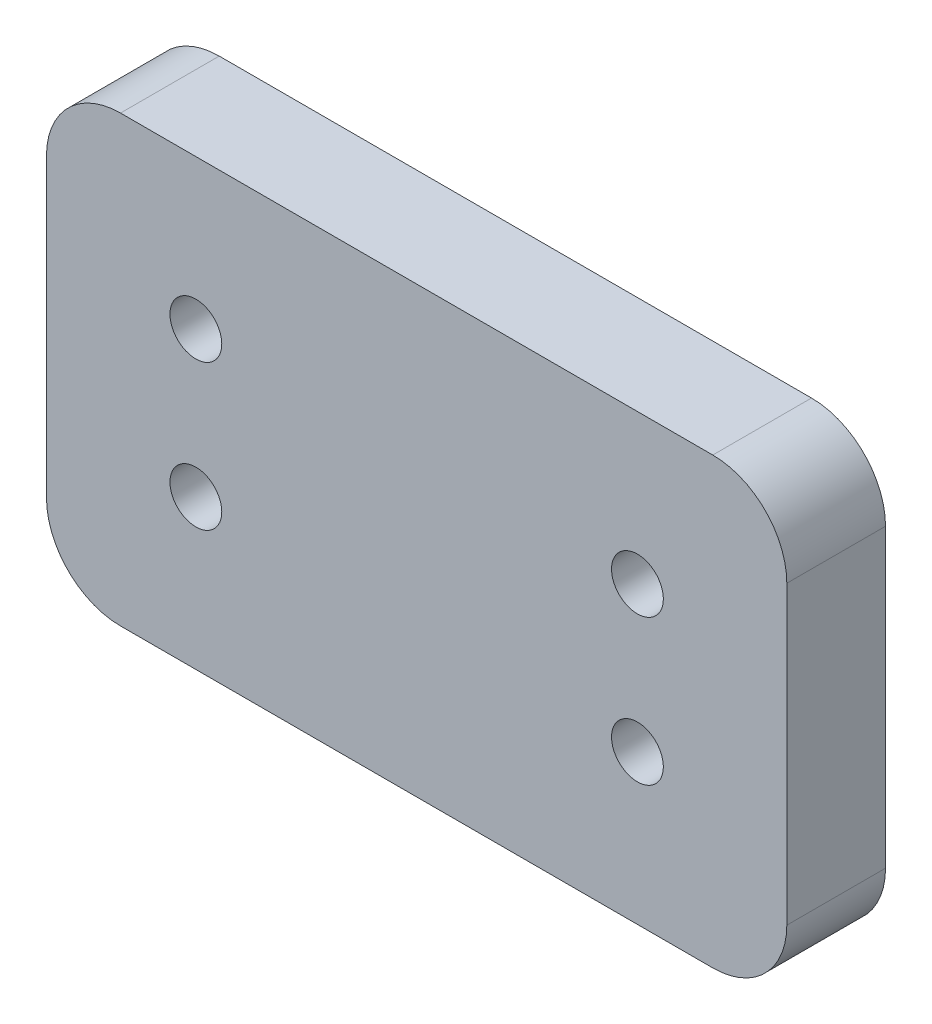
SolidWorks part; units mm, degrees
ref_plane "Plan de face" through (0, 0, 0) normal (0, 0, 1) x (1, 0, 0)
ref_plane "Plan de dessus" through (0, 0, 0) normal (0, 1, 0) x (1, 0, 0)
ref_plane "Plan de droite" through (0, 0, 0) normal (1, 0, 0) x (0, 0, -1)
sketch "Esquisse1" plane through (0, 0, 0) normal (0, 0, 1) x (1, 0, 0)
  line L1 (0, 0) -> (30, 0)
  line L2 (0, 0) -> (0, 18)
  line L3 (0, 18) -> (30, 18)
  line L4 (30, 0) -> (30, 18)
  dimension "D1" = 30
  dimension "D2" = 18
extrude "Boss.-Extru.1" add sketch "Esquisse1" along normal blind 4
fillet "Congé1" radius 3 4 edges at (0, 0, 2) (30, 0, 2) (30, 18, 2) (0, 18, 2)
sketch "Esquisse2" plane through (0, 0, 4) normal (0, 0, 1) x (1, 0, 0)
  line L0 (27, 18) -> (3, 18) construction
  line L1 (6.053, 11.947) -> (23.947, 11.947) construction
  line L2 (6.053, 11.947) -> (6.053, 6.053) construction
  line L3 (6.053, 6.053) -> (23.947, 6.053) construction
  line L4 (23.947, 11.947) -> (23.947, 6.053) construction
  line L5 (3, 0) -> (27, 0) construction
  line L6 (0, 15) -> (0, 3) construction
  line L7 (30, 3) -> (30, 15) construction
  circle A0 centre (6.053, 11.947) radius 1.05
  circle A1 centre (6.053, 6.053) radius 1.05
  circle A2 centre (23.947, 11.947) radius 1.05
  circle A3 centre (23.947, 6.053) radius 1.05
  dimension "D1" = 6.053
  dimension "D2" = 6.053
  dimension "D3" = 6.053
  dimension "D4" = 6.053
extrude "Enlèv. mat.-Extru.1" cut sketch "Esquisse2" against normal through all
